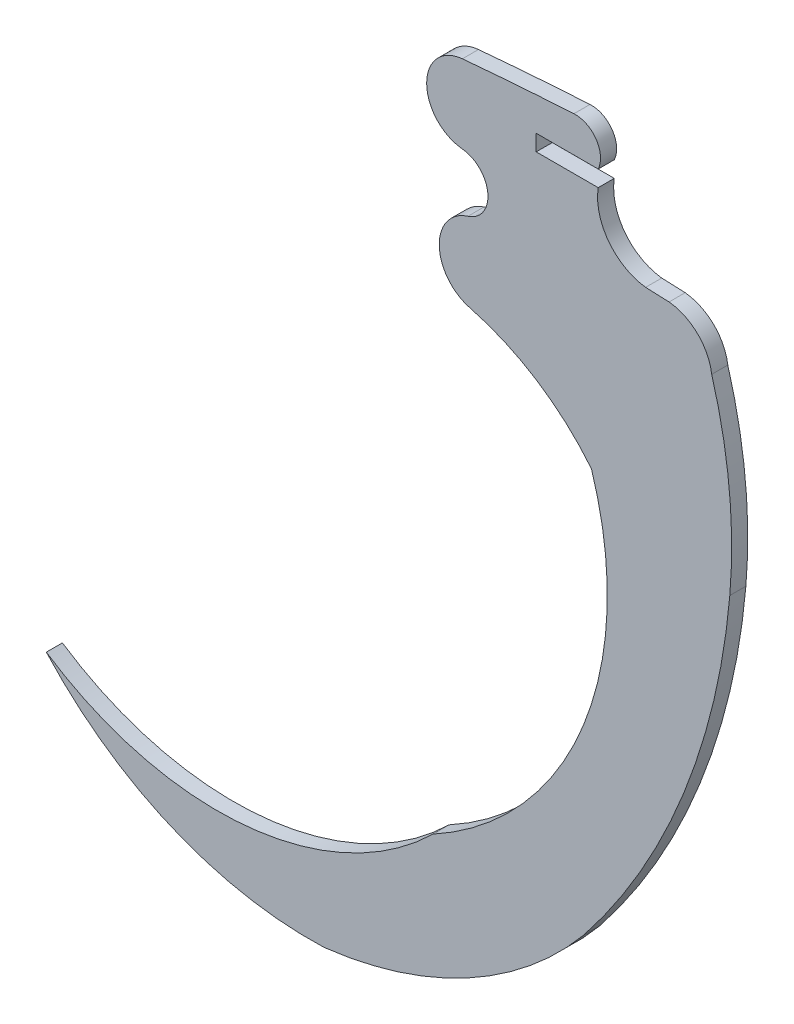
SolidWorks part; units mm, degrees
ref_plane "Front Plane" through (0, 0, 0) normal (0, 0, 1) x (1, 0, 0)
ref_plane "Top Plane" through (0, 0, 0) normal (0, 1, 0) x (1, 0, 0)
ref_plane "Right Plane" through (0, 0, 0) normal (1, 0, 0) x (0, 0, -1)
sketch "Sketch1" plane through (0, 0, 0) normal (0, 0, 1) x (1, 0, 0)
  line L0 (8.0985, 11.8597) -> (5.8774, 11.9499)
  line L1 (1.3788, 17.8827) -> (-4.4945, 17.8819)
  line L2 (-4.4945, 17.8819) -> (-4.4945, 19.4089)
  line L3 (-4.4945, 19.4089) -> (1.3809, 19.4089)
  arc A0 (-0.9218, 22.7983) -> (-11.4899, 22.0223) centre (18.5641, -314.933) ccw
  arc A1 (-11.4899, 22.0223) -> (-11.5098, 14.6225) centre (-11.1608, 18.3215) ccw
  arc A2 (-10.9654, 9.362) -> (-11.5098, 14.6225) centre (-11.7628, 11.9379) ccw
  arc A3 (-10.9654, 9.362) -> (-10.8029, 1.9473) centre (-9.8275, 5.6778) ccw
  arc A4 (0.7391, -5.5084) -> (-10.8029, 1.9473) centre (-16.3589, -19.3156) ccw
  arc A5 (13.8536, -9.3552) -> (0, -44.1568) centre (-51.0453, -3.6788) cw
  arc A6 (-24.5856, -57.4597) -> (0, -44.1568) centre (-28.9041, -20.1085) ccw
  arc A7 (13.8536, -9.3552) -> (12.1391, 7.9385) centre (-32.9399, -5.2624) ccw
  arc A8 (12.1391, 7.9385) -> (8.0985, 11.8597) centre (7.6376, 7.3424) ccw
  arc A9 (1.3788, 17.8827) -> (5.8774, 11.9499) centre (6.4974, 17.0919) ccw
  arc A10 (1.3809, 19.4089) -> (-0.9218, 22.7983) centre (-0.7849, 20.4144) ccw
  arc A11 (0.7391, -5.5084) -> (-14.2759, -43.0043) centre (-29.4589, -15.1701) cw
  arc A12 (-14.2759, -43.0043) -> (-50.9216, -46.3915) centre (-34.6892, -22.0821) cw
  arc A14 (-50.9216, -46.3915) -> (-24.5856, -57.4597) centre (-25.8781, -23.6686) ccw
extrude "Boss-Extrude1" add sketch "Sketch1" along normal blind 1.524
